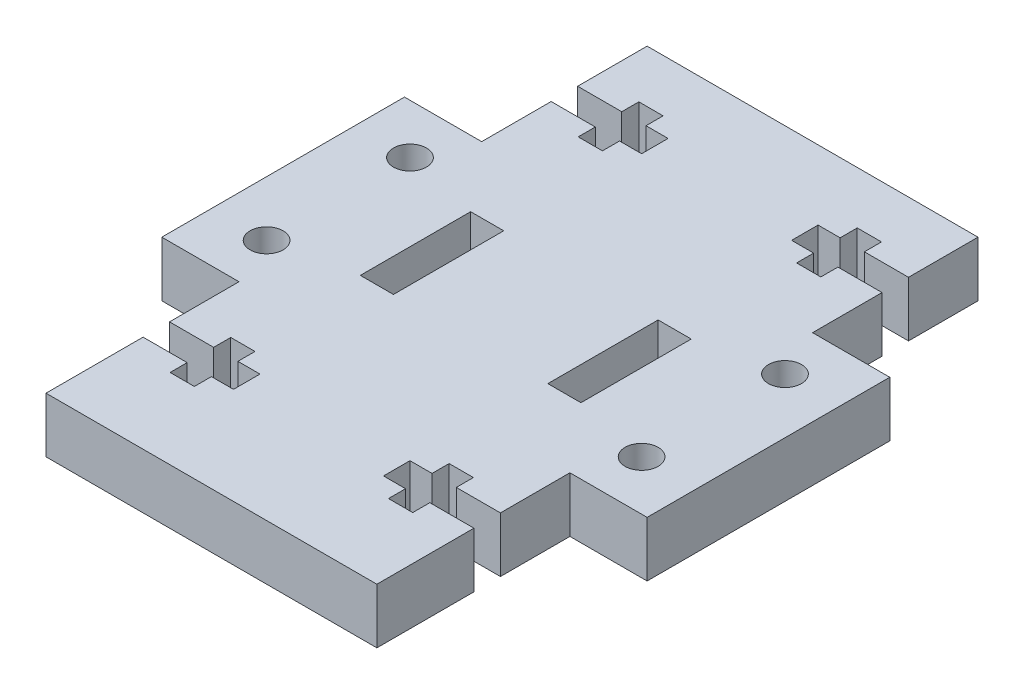
SolidWorks part; units mm, degrees
material "Acrylic (Medium-high impact)"
ref_plane "Front Plane" through (0, 0, 0) normal (0, 0, 1) x (1, 0, 0)
ref_plane "Top Plane" through (0, 0, 0) normal (0, 1, 0) x (1, 0, 0)
ref_plane "Right Plane" through (0, 0, 0) normal (1, 0, 0) x (0, 0, -1)
sketch "Sketch2" plane through (0, 0, 0) normal (0, 1, 0) x (1, 0, 0)
  line L0 (9.6071, -57.7264) -> (39.6071, -57.7264)
  line L1 (39.6071, -3.2264) -> (39.6071, -18.2264)
  line L2 (39.6071, -18.2264) -> (46.6071, -18.2264)
  line L3 (46.6071, -18.2264) -> (46.6071, -40.2264)
  line L4 (46.6071, -40.2264) -> (39.6071, -40.2264)
  line L5 (39.6071, -40.2264) -> (39.6071, -57.7264)
  line L6 (39.6071, -3.2264) -> (9.6071, -3.2264)
  line L7 (24.6071, -3.2264) -> (24.6071, -57.7264) construction
  line L8 (31.6071, -34.2264) -> (34.6071, -34.2264)
  line L9 (34.6071, -34.2264) -> (34.6071, -24.2264)
  line L10 (9.6071, -40.2264) -> (9.6071, -57.7264)
  line L11 (9.6071, -3.2264) -> (9.6071, -18.2264)
  line L13 (34.6071, -24.2264) -> (31.6071, -24.2264)
  line L14 (31.6071, -24.2264) -> (31.6071, -34.2264)
  line L16 (17.6071, -24.2264) -> (17.6071, -34.2264)
  line L17 (14.6071, -24.2264) -> (17.6071, -24.2264)
  line L18 (14.6071, -34.2264) -> (14.6071, -24.2264)
  line L19 (17.6071, -34.2264) -> (14.6071, -34.2264)
  line L20 (2.6071, -40.2264) -> (9.6071, -40.2264)
  line L21 (2.6071, -18.2264) -> (2.6071, -40.2264)
  line L22 (9.6071, -18.2264) -> (2.6071, -18.2264)
  line L29 (46.6071, -29.2264) -> (31.6071, -29.2264) construction
  circle A0 centre (41.6071, -22.7264) radius 1.5
  circle A1 centre (41.6071, -35.7264) radius 1.5
  circle A2 centre (7.6071, -35.7264) radius 1.5
  circle A3 centre (7.6071, -22.7264) radius 1.5
  point P12 (31.6071, -29.2264)
  point P15 (46.6071, -29.2264)
  dimension "D11" = 3
  dimension "D1" = 22
  dimension "D2" = 15
  dimension "D3" = 17.5
  dimension "D4" = 22
  dimension "D5" = 7
  dimension "D6" = 10
  dimension "D7" = 6.5
  dimension "D8" = 3
  dimension "D9" = 12
  dimension "D12" = 5
extrude "Boss-Extrude2" add sketch "Sketch2" along normal blind 5
sketch "Sketch3" plane through (0, 5, 0) normal (0, 1, 0) x (-1, 0, 0)
  line L0 (-39.6071, 18.2264) -> (-39.6071, 3.2264) construction
  line L1 (-39.6071, 57.7264) -> (-39.6071, 40.2264) construction
  line L2 (-39.6071, 46.5264) -> (-35.6071, 46.5264)
  line L3 (-39.6071, 9.5264) -> (-35.6071, 9.5264)
  line L4 (-35.6071, 9.5264) -> (-35.6071, 7.9764)
  line L5 (-35.6071, 7.9764) -> (-33.4071, 7.9764)
  line L6 (-33.4071, 7.9764) -> (-33.4071, 9.5264)
  line L7 (-33.4071, 9.5264) -> (-31.4071, 9.5264)
  line L8 (-31.4071, 9.5264) -> (-31.4071, 11.9264)
  line L9 (-39.6071, 9.5264) -> (-39.6071, 11.9264)
  line L10 (-33.4071, 11.9264) -> (-31.4071, 11.9264)
  line L11 (-33.4071, 13.4764) -> (-33.4071, 11.9264)
  line L12 (-35.6071, 13.4764) -> (-33.4071, 13.4764)
  line L13 (-35.6071, 11.9264) -> (-35.6071, 13.4764)
  line L14 (-39.6071, 11.9264) -> (-35.6071, 11.9264)
  line L15 (-24.6071, 3.2264) -> (-24.6071, 57.7264) construction
  line L16 (-39.6071, 3.2264) -> (-9.6071, 3.2264) construction
  line L17 (-9.6071, 57.7264) -> (-39.6071, 57.7264) construction
  line L18 (-39.6071, 48.9264) -> (-35.6071, 48.9264)
  line L19 (-35.6071, 48.9264) -> (-35.6071, 50.4764)
  line L20 (-39.6071, 46.5264) -> (-39.6071, 48.9264)
  line L21 (-35.6071, 46.5264) -> (-35.6071, 44.9764)
  line L22 (-35.6071, 44.9764) -> (-33.4071, 44.9764)
  line L23 (-33.4071, 44.9764) -> (-33.4071, 46.5264)
  line L24 (-33.4071, 46.5264) -> (-31.4071, 46.5264)
  line L25 (-31.4071, 46.5264) -> (-31.4071, 48.9264)
  line L26 (-33.4071, 48.9264) -> (-31.4071, 48.9264)
  line L27 (-33.4071, 50.4764) -> (-33.4071, 48.9264)
  line L28 (-35.6071, 50.4764) -> (-33.4071, 50.4764)
  line L29 (-13.6071, 50.4764) -> (-15.8071, 50.4764)
  line L30 (-15.8071, 50.4764) -> (-15.8071, 48.9264)
  line L31 (-15.8071, 48.9264) -> (-17.8071, 48.9264)
  line L32 (-17.8071, 46.5264) -> (-17.8071, 48.9264)
  line L33 (-15.8071, 46.5264) -> (-17.8071, 46.5264)
  line L34 (-15.8071, 44.9764) -> (-15.8071, 46.5264)
  line L35 (-13.6071, 44.9764) -> (-15.8071, 44.9764)
  line L36 (-13.6071, 46.5264) -> (-13.6071, 44.9764)
  line L37 (-9.6071, 46.5264) -> (-9.6071, 48.9264)
  line L38 (-13.6071, 48.9264) -> (-13.6071, 50.4764)
  line L39 (-9.6071, 48.9264) -> (-13.6071, 48.9264)
  line L40 (-9.6071, 11.9264) -> (-13.6071, 11.9264)
  line L41 (-13.6071, 11.9264) -> (-13.6071, 13.4764)
  line L42 (-13.6071, 13.4764) -> (-15.8071, 13.4764)
  line L43 (-15.8071, 13.4764) -> (-15.8071, 11.9264)
  line L44 (-15.8071, 11.9264) -> (-17.8071, 11.9264)
  line L45 (-9.6071, 9.5264) -> (-9.6071, 11.9264)
  line L46 (-17.8071, 9.5264) -> (-17.8071, 11.9264)
  line L47 (-15.8071, 9.5264) -> (-17.8071, 9.5264)
  line L48 (-15.8071, 7.9764) -> (-15.8071, 9.5264)
  line L49 (-13.6071, 7.9764) -> (-15.8071, 7.9764)
  line L50 (-13.6071, 9.5264) -> (-13.6071, 7.9764)
  line L51 (-9.6071, 9.5264) -> (-13.6071, 9.5264)
  line L52 (-9.6071, 46.5264) -> (-13.6071, 46.5264)
  point P0 (-39.6071, 10.7264)
  point P1 (-39.6071, 10.7264)
  point P15 (-31.4071, 10.7264)
  point P61 (-17.8071, 10.7264)
  point P62 (-9.6071, 10.7264)
  dimension "D1" = 2.4
  dimension "D2" = 5.5
  dimension "D3" = 2.2
  dimension "D4" = 2
  dimension "D5" = 4
extrude "Cut-Extrude1" cut sketch "Sketch3" against normal through all
